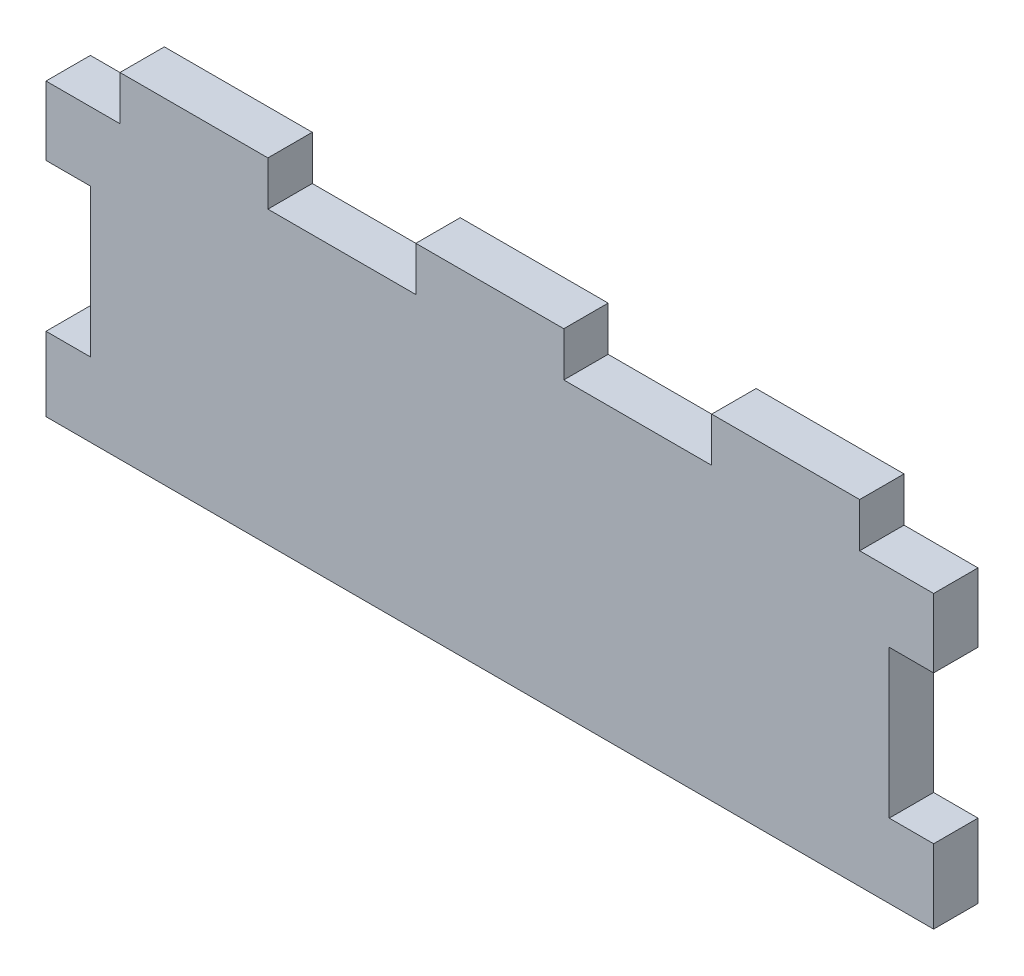
SolidWorks part; units mm, degrees
ref_plane "Front Plane" through (0, 0, 0) normal (0, 0, 1) x (1, 0, 0)
ref_plane "Top Plane" through (0, 0, 0) normal (0, 1, 0) x (1, 0, 0)
ref_plane "Right Plane" through (0, 0, 0) normal (1, 0, 0) x (0, 0, -1)
sketch "Sketch1" plane through (0, 0, 0) normal (0, 0, 1) x (1, 0, 0)
  line L1 (0, 0) -> (120, 0)
  line L2 (0, 0) -> (0, -45.3)
  line L3 (0, -45.3) -> (120, -45.3)
  line L4 (120, 0) -> (120, -45.3)
  dimension "D1" = 120
  dimension "D2" = 45.3
extrude "Boss-Extrude1" add sketch "Sketch1" along normal blind 6
sketch "Sketch2" plane through (0, 0, 6) normal (0, 0, 1) x (1, 0, 0)
  line L0 (120, 0) -> (0, 0) construction
  line L1 (0, 0) -> (10, 0)
  line L2 (0, 0) -> (0, -45.3) construction
  line L3 (0, 0) -> (0, -6)
  line L4 (0, -6) -> (10, -6)
  line L5 (10, 0) -> (10, -6)
  line L6 (30, 0) -> (50, 0)
  line L7 (30, 0) -> (30, -6)
  line L8 (30, -6) -> (50, -6)
  line L9 (50, 0) -> (50, -6)
  line L10 (70, 0) -> (70, -6)
  line L11 (90, -6) -> (70, -6)
  line L12 (90, 0) -> (90, -6)
  line L13 (90, 0) -> (70, 0)
  line L14 (110, 0) -> (110, -6)
  line L15 (120, -6) -> (110, -6)
  line L16 (120, 0) -> (120, -6)
  line L17 (120, 0) -> (110, 0)
  line L18 (60, 5.4018) -> (60, -69.7728) construction
  line L19 (0, -45.3) -> (120, -45.3) construction
  line L20 (114, -15.3) -> (114, -35.3)
  line L25 (0, -15.3) -> (6, -15.3)
  line L26 (0, -15.3) -> (0, -35.3)
  line L27 (0, -35.3) -> (6, -35.3)
  line L28 (6, -15.3) -> (6, -35.3)
  line L29 (120, -35.3) -> (114, -35.3)
  line L30 (120, -15.3) -> (120, -35.3)
  line L31 (114, -15.3) -> (120, -15.3)
  point P23 (60, -45.3)
  dimension "D6" = 10
  dimension "D1" = 10
  dimension "D2" = 6
  dimension "D3" = 20
  dimension "D4" = 20
extrude "Cut-Extrude1" cut sketch "Sketch2" against normal blind 6
equation "\"Material Thickness\"= 6mm"
equation "\"D1@Boss-Extrude1\"=\"Material Thickness\""
equation "\"D2@Sketch1\"=39.3mm+\"Material Thickness\""
equation "\"D1@Cut-Extrude1\"=\"Material Thickness\""
equation "\"D2@Sketch2\"=\"Material Thickness\""
equation "\"D4@Sketch2\"=\"D3@Sketch2\""
